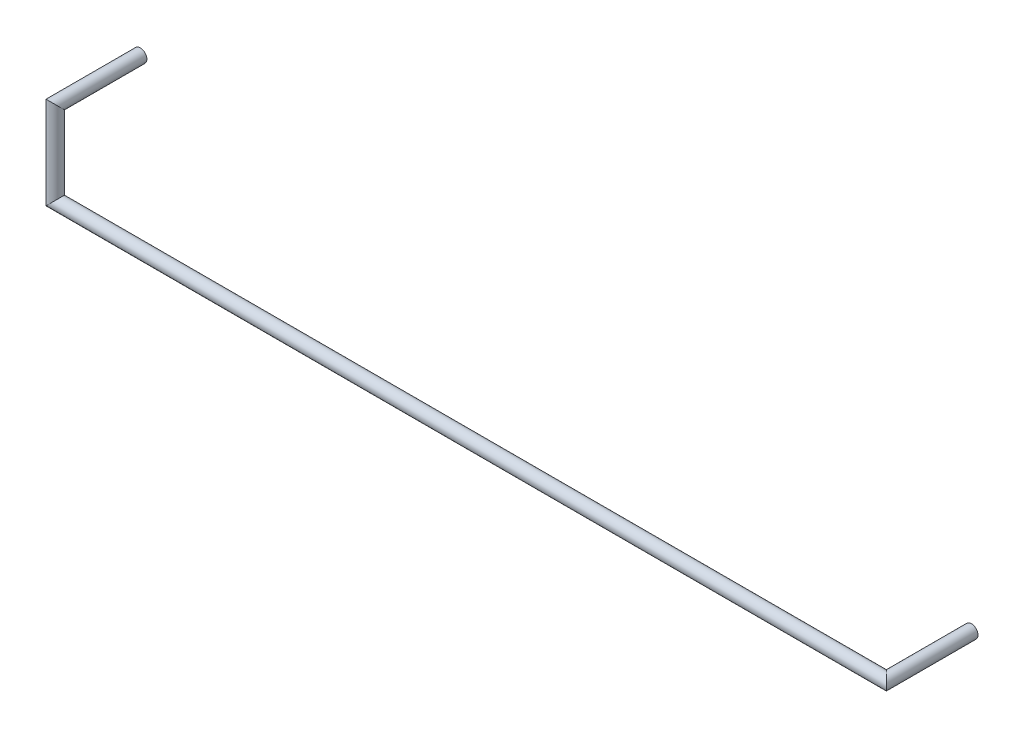
SolidWorks part; units mm, degrees
ref_plane "Front Plane" through (0, 0, 0) normal (0, 0, 1) x (1, 0, 0)
ref_plane "Top Plane" through (0, 0, 0) normal (0, 1, 0) x (1, 0, 0)
ref_plane "Right Plane" through (0, 0, 0) normal (1, 0, 0) x (0, 0, -1)
sketch3d "3DSketch3"
  line L0 (0, 0, 0) -> (0, 0, 2.6)
  line L1 (0, 0, 2.6) -> (0, -2.54, 2.6)
  line L2 (0, -2.54, 2.6) -> (25.4, -2.54, 2.6)
  line L3 (25.4, -2.54, 2.6) -> (25.4, -2.54, 0)
  dimension "D2" = 2.6
  dimension "D1" = 2.6
  dimension "D4" = 25.4
  dimension "D3" = 2.54
sweep "Sweep1" add path "3DSketch3" circular profile diameter 0.4 parameters "D3"=0.4
equation "\"D2@3DSketch3\"=\"D1@3DSketch3\""
equation "\"D4@3DSketch3\"=2.54*10"
equation "\"D3@3DSketch3\"=2.54"
